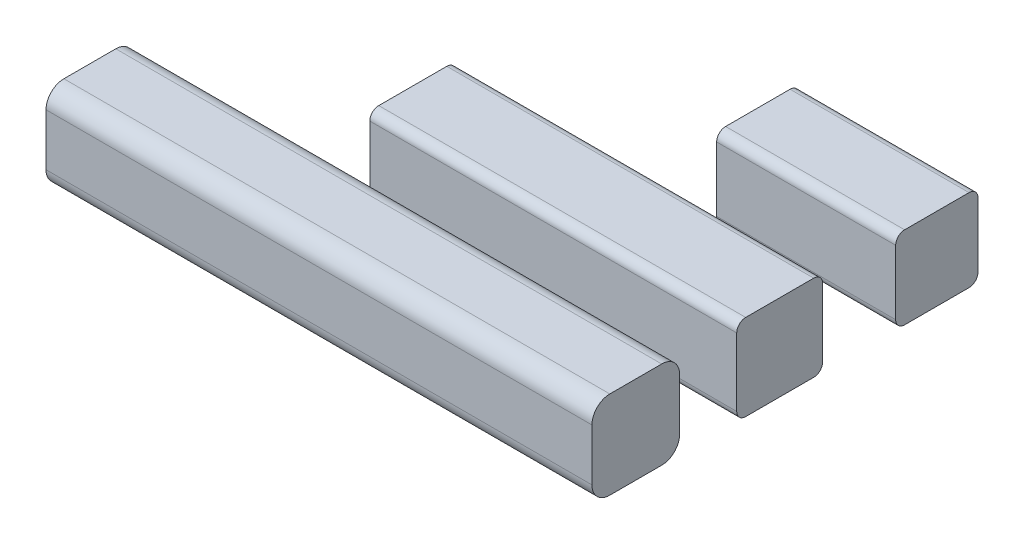
SolidWorks part; units mm, degrees
ref_plane "前视基准面" through (0, 0, 0) normal (0, 0, 1) x (1, 0, 0)
ref_plane "上视基准面" through (0, 0, 0) normal (0, 1, 0) x (1, 0, 0)
ref_plane "右视基准面" through (0, 0, 0) normal (1, 0, 0) x (0, 0, -1)
sketch "草图1" plane through (0, 0, 0) normal (0, 1, 0) x (1, 0, 0)
  line L1 (-12.2772, 15.4322) -> (-7.2772, 15.4322)
  line L2 (-12.2772, 15.4322) -> (-12.2772, 20.4322)
  line L3 (-12.2772, 20.4322) -> (-7.2772, 20.4322)
  line L4 (-7.2772, 15.4322) -> (-7.2772, 20.4322)
  line L5 (-12.2772, 15.4322) -> (-7.2772, 20.4322) construction
  line L6 (-12.2772, 20.4322) -> (-7.2772, 15.4322) construction
  circle A0 centre (-9.7772, 17.9322) radius 4.9
  dimension "D1" = 9.8
  dimension "D2" = 5
  dimension "D3" = 5
extrude "凸台-拉伸1" add sketch "草图1" along normal blind 5
sketch "草图2" plane through (0, 0, 0) normal (0, 1, 0) x (1, 0, 0)
  line L0 (-20.4935, 24.5269) -> (-10.4935, 24.5269)
  line L1 (-10.4935, 24.5269) -> (-10.4935, 29.5269)
  line L2 (-10.4935, 29.5269) -> (-20.4935, 29.5269)
  line L3 (-20.4935, 29.5269) -> (-20.4935, 24.5269)
  dimension "D1" = 10
  dimension "D2" = 5
extrude "凸台-拉伸2" add sketch "草图2" along normal blind 5 separate body
sketch "草图3" plane through (0, 5, 0) normal (0, 1, 0) x (1, 0, 0)
  circle A0 centre (-9.7772, 17.9322) radius 5.9149
extrude "切除-拉伸1" cut sketch "草图3" against normal blind 10
sketch "草图4" plane through (-20.4935, 0, 0) normal (-1, 0, 0) x (0, 0, 1)
  line L0 (-24.5269, 5) -> (-24.5269, 0) construction
  line L1 (-29.5269, 4.9) -> (-29.5269, 5)
  line L2 (-24.6269, 0) -> (-24.5269, 0)
  line L3 (-29.5269, 4.9) -> (-24.6269, 4.9)
  line L4 (-24.6269, 0) -> (-24.6269, 4.9)
  line L8 (-29.5269, 5) -> (-24.5269, 5)
  line L9 (-24.5269, 0) -> (-24.5269, 5)
  dimension "D1" = 4.9
  dimension "D2" = 0.1
extrude "切除-拉伸2" cut sketch "草图4" against normal blind 10
sketch "草图5" plane through (0, 0, 0) normal (1, 0, 0) x (0, 0, -1)
  line L2 (32.7248, 0) -> (37.5248, 0)
  line L3 (32.7248, 0) -> (32.7248, 4.8)
  line L4 (32.7248, 4.8) -> (37.5248, 4.8)
  line L5 (37.5248, 0) -> (37.5248, 4.8)
  line L6 (41.6044, 0) -> (46.2044, 0)
  line L7 (41.6044, 0) -> (41.6044, 4.6)
  line L8 (41.6044, 4.6) -> (46.2044, 4.6)
  line L9 (46.2044, 0) -> (46.2044, 4.6)
  line L10 (48.6704, 0) -> (53.1704, 0)
  line L11 (48.6704, 0) -> (48.6704, 4.5)
  line L12 (48.6704, 4.5) -> (53.1704, 4.5)
  line L13 (53.1704, 0) -> (53.1704, 4.5)
  dimension "D1" = 4.8
  dimension "D2" = 4.6
  dimension "D4" = 4.5
  dimension "D5" = 4.5
extrude "凸台-拉伸3" add sketch "草图5" along normal blind 10 separate body
fillet "圆角1" radius 0.5 4 edges at (-15.4935, 0, -29.5269) (-15.4935, 0, -24.6269) (-15.4935, 4.9, -29.5269) (-15.4935, 4.9, -24.6269)
fillet "圆角2" radius 0.5 4 edges at (5, 4.8, -37.5248) (5, 0, -37.5248) (5, 0, -32.7248) (5, 4.8, -32.7248)
fillet "圆角3" radius 0.5 4 edges at (5, 0, -41.6044) (5, 0, -46.2044) (5, 4.6, -41.6044) (5, 4.6, -46.2044)
fillet "圆角4" radius 0.5 4 edges at (5, 0, -48.6704) (5, 0, -53.1704) (5, 4.5, -48.6704) (5, 4.5, -53.1704)
sketch "草图6" plane through (-10.4935, 0, 0) normal (1, 0, 0) x (0, 0, -1)
  line L1 (24.6269, 4.9) -> (29.5269, 4.9)
  line L2 (24.6269, 4.9) -> (24.6269, 0)
  line L3 (24.6269, 0) -> (29.5269, 0)
  line L4 (29.5269, 4.9) -> (29.5269, 0)
  line L5 (24.6269, 4.9) -> (29.5269, 0) construction
  line L6 (24.6269, 0) -> (29.5269, 4.9) construction
  point P0 (27.0769, 2.45)
extrude "凸台-拉伸4" add sketch "草图6" along normal blind 20.5
fillet "圆角5" radius 1 4 edges at (-0.2435, 0, -24.6269) (-0.2435, 0, -29.5269) (-0.2435, 4.9, -29.5269) (-0.2435, 4.9, -24.6269)
sketch "草图8" plane through (0, 0, 0) normal (-1, 0, 0) x (0, 0, 1)
  line L4 (-33.2248, 4.8) -> (-37.0248, 4.8)
  line L5 (-37.5248, 4.3) -> (-37.5248, 0.5)
  line L6 (-37.0248, 0) -> (-33.2248, 0)
  line L7 (-32.7248, 0.5) -> (-32.7248, 4.3)
  line L8 (-33.2248, 4.8) -> (-37.0248, 4.8)
  line L9 (-37.5248, 4.3) -> (-37.5248, 0.5)
  line L10 (-37.0248, 0) -> (-33.2248, 0)
  line L11 (-32.7248, 0.5) -> (-32.7248, 4.3)
  arc A4 (-37.0248, 4.8) -> (-37.5248, 4.3) centre (-37.0248, 4.3) ccw
  arc A5 (-37.5248, 0.5) -> (-37.0248, 0) centre (-37.0248, 0.5) ccw
  arc A6 (-33.2248, 0) -> (-32.7248, 0.5) centre (-33.2248, 0.5) ccw
  arc A7 (-32.7248, 4.3) -> (-33.2248, 4.8) centre (-33.2248, 4.3) ccw
  arc A8 (-37.0248, 4.8) -> (-37.5248, 4.3) centre (-37.0248, 4.3) ccw
  arc A9 (-37.5248, 0.5) -> (-37.0248, 0) centre (-37.0248, 0.5) ccw
  arc A10 (-33.2248, 0) -> (-32.7248, 0.5) centre (-33.2248, 0.5) ccw
  arc A11 (-32.7248, 4.3) -> (-33.2248, 4.8) centre (-33.2248, 4.3) ccw
  dimension "D1" = 0
extrude "凸台-拉伸5" add sketch "草图8" along normal blind 10.5
sketch "草图9" plane through (0, 0, 0) normal (-1, 0, 0) x (0, 0, 1)
  circle A0 centre (-50.9868, 2.3556) radius 3.4026
extrude "切除-拉伸3" cut sketch "草图9" against normal blind 10.5
